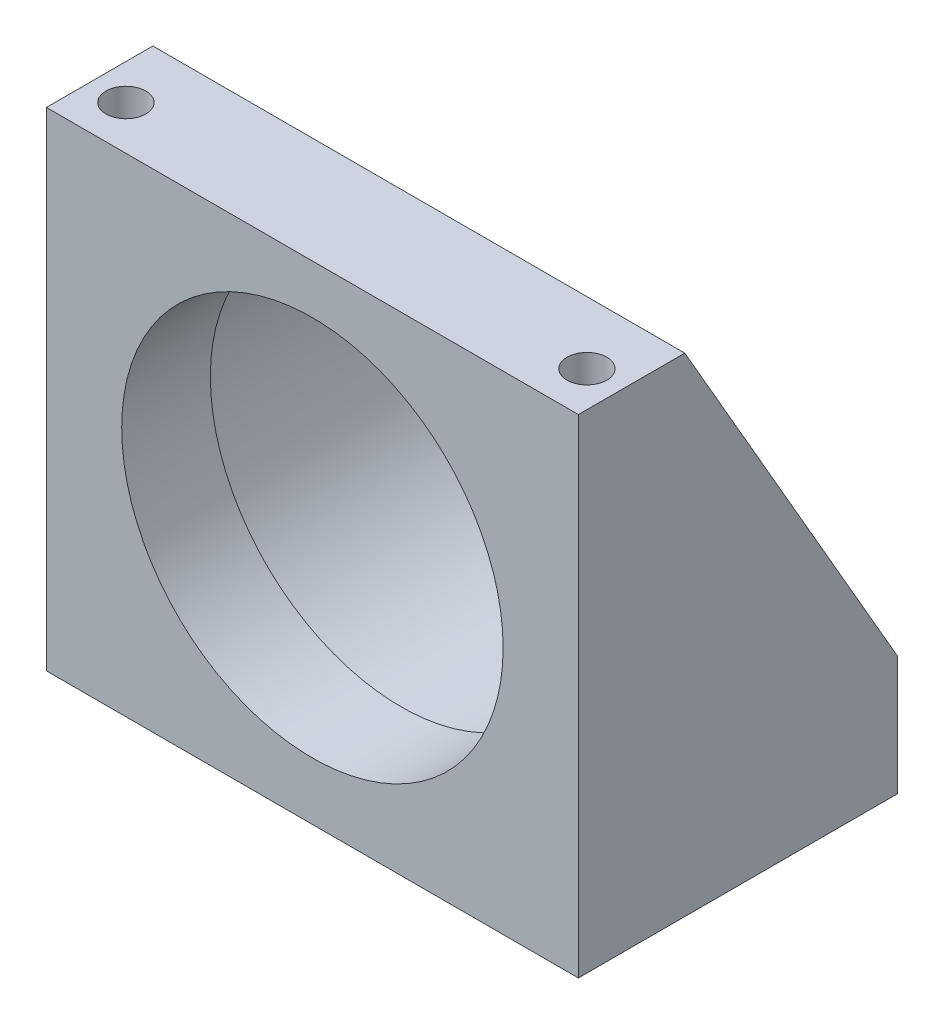
SolidWorks part; units mm, degrees
material "Alloy Steel"
ref_plane "Front Plane" through (0, 0, 0) normal (0, 0, 1) x (1, 0, 0)
ref_plane "Top Plane" through (0, 0, 0) normal (0, 1, 0) x (1, 0, 0)
ref_plane "Right Plane" through (0, 0, 0) normal (1, 0, 0) x (0, 0, -1)
sketch "Sketch1" plane through (0, 0, 0) normal (0, 0, 1) x (1, 0, 0)
  line L1 (-47.625, 87.376) -> (47.625, 87.376)
  line L2 (-47.625, 87.376) -> (-47.625, 0)
  line L3 (-47.625, 0) -> (47.625, 0)
  line L4 (47.625, 87.376) -> (47.625, 0)
  circle A0 centre (0, 44.45) radius 34.1503
  dimension "D4" = 68.3006
  dimension "D1" = 95.25
  dimension "D2" = 87.376
  dimension "D3" = 44.45
extrude "Extrude1" add sketch "Sketch1" against normal blind 57.15
sketch "Sketch2" plane through (47.625, 0, 0) normal (1, 0, 0) x (0, 0, -1)
  line L0 (19.05, 87.376) -> (57.15, 21.336)
  line L1 (0, 0) -> (0, 87.376) construction
  line L2 (57.15, 0) -> (0, 0) construction
  line L4 (0, 87.376) -> (0, 0)
  line L5 (0, 0) -> (57.15, 0)
  line L6 (57.15, 0) -> (57.15, 87.376)
  line L7 (57.15, 87.376) -> (0, 87.376)
  line L10 (57.15, 21.336) -> (57.15, 87.376)
  line L11 (57.15, 87.376) -> (19.05, 87.376)
  dimension "D2" = 19.05
  dimension "D3" = 21.336
  dimension "D1" = 0
extrude "Cut-Extrude1" cut sketch "Sketch2" against normal through all
sketch "Sketch3" plane through (0, 0, -57.15) normal (0, 0, -1) x (-1, 0, 0)
  circle A0 centre (0, 44.45) radius 36.576
  dimension "D1" = 73.152
extrude "Cut-Extrude2" cut sketch "Sketch3" against normal offset from surface (41.275 mm away) 15.875 up to face at (34.1503, 44.45, 0)
fillet "Fillet1" radius 1.524 1 edges at (36.576, 44.45, -15.875)
hole_wizard "Hole1" positions "Sketch5" profile "Sketch4" legacy end condition up to next
sketch "Sketch5" plane through (0, 87.376, 0) normal (0, 1, 0) x (-1, 0, 0)
  line L0 (-47.625, -19.05) -> (-47.625, 0) construction
  line L1 (-47.625, 0) -> (47.625, 0) construction
  point P0 (41.275, -7.874)
  point P1 (-41.275, -7.874)
  dimension "D1" = 6.35
  dimension "D2" = 7.874
  dimension "D3" = 82.55
sketch "Sketch4" plane through (-41.275, 87.376, -7.874) normal (1, 0, 0) x (0, 0, 1)
  line L0 (0, 0) -> (0, 87.376)
  line L1 (0, 87.376) -> (3.5687, 87.376)
  line L2 (3.5687, 87.376) -> (3.5687, 0)
  line L3 (3.5687, 0) -> (0, 0)
  line L4 (0, 110) -> (0, -10) construction
  dimension "Diameter" = 7.1374
  dimension "Depth" = 87.376
